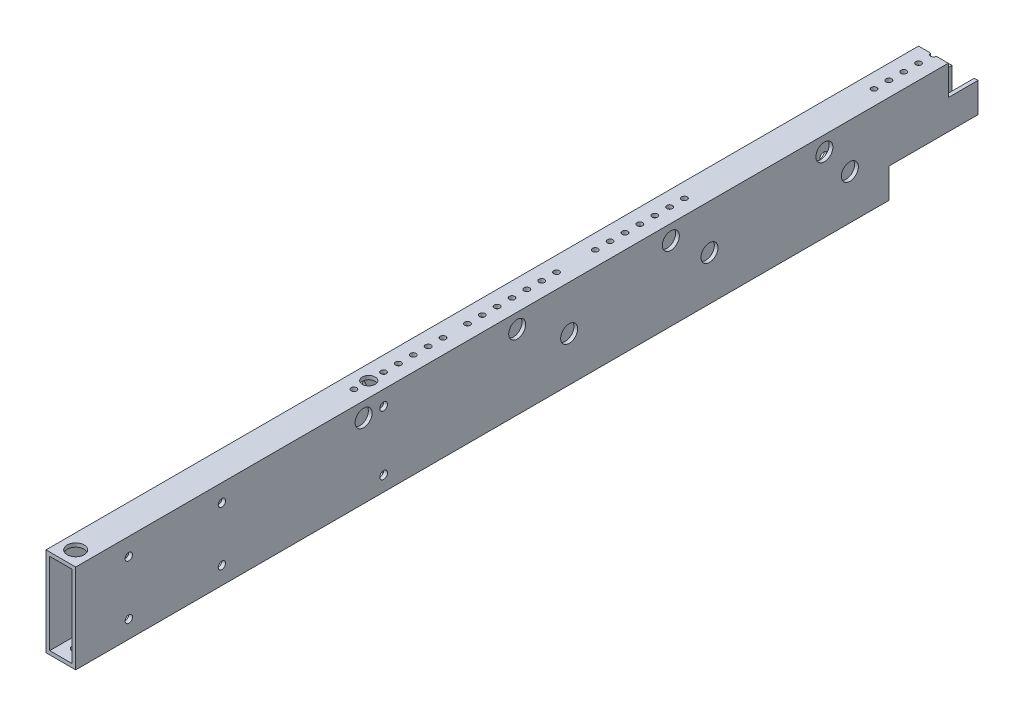
SolidWorks part; units mm, degrees
ref_plane "Front Plane" through (0, 0, 0) normal (0, 0, 1) x (1, 0, 0)
ref_plane "Top Plane" through (0, 0, 0) normal (0, 1, 0) x (1, 0, 0)
ref_plane "Right Plane" through (0, 0, 0) normal (1, 0, 0) x (0, 0, -1)
sketch "Sketch1" plane through (0, 0, 0) normal (0, 0, 1) x (1, 0, 0)
  line L1 (-12.7, -38.1) -> (12.7, -38.1)
  line L2 (-12.7, -38.1) -> (-12.7, 38.1)
  line L3 (-12.7, 38.1) -> (12.7, 38.1)
  line L4 (12.7, -38.1) -> (12.7, 38.1)
  line L5 (-12.7, -38.1) -> (12.7, 38.1) construction
  line L6 (-12.7, 38.1) -> (12.7, -38.1) construction
  point P0 (0, 0)
  dimension "D1" = 25.4
  dimension "D2" = 76.2
extrude "Boss-Extrude1" add sketch "Sketch1" along normal mid plane 771.398
shell "Shell1" thickness 3.175
sketch "Sketch2" plane through (12.7, 0, 0) normal (1, 0, 0) x (0, 0, -1)
  line L1 (385.699, -38.1) -> (309.499, -38.1)
  line L2 (385.699, -38.1) -> (385.699, -12.7)
  line L3 (385.699, -12.7) -> (309.499, -12.7)
  line L4 (309.499, -38.1) -> (309.499, -12.7)
  dimension "D1" = 25.4
  dimension "D2" = 76.2
extrude "Cut-Extrude1" cut sketch "Sketch2" against normal through all
sketch "Sketch3" plane through (12.7, 0, 0) normal (1, 0, 0) x (0, 0, -1)
  line L1 (385.699, 38.1) -> (360.299, 38.1)
  line L2 (385.699, 38.1) -> (385.699, 12.7)
  line L3 (385.699, 12.7) -> (360.299, 12.7)
  line L4 (360.299, 38.1) -> (360.299, 12.7)
  dimension "D1" = 25.4
extrude "Cut-Extrude2" cut sketch "Sketch3" against normal through all
sketch "Sketch4" plane through (0, 38.1, 0) normal (0, 1, 0) x (1, 0, 0)
  line L0 (-12.7, 360.299) -> (12.7, 360.299) construction
  circle A0 centre (0, 147.3945) radius 2.3812
  circle A1 centre (0, 134.6945) radius 2.3812
  circle A2 centre (0, 121.9945) radius 2.3812
  circle A3 centre (0, 109.2945) radius 2.3812
  circle A4 centre (0, 96.5945) radius 2.3812
  circle A5 centre (0, 83.8945) radius 2.3812
  circle A6 centre (0, 71.1945) radius 2.3812
  circle A7 centre (0, 38.0987) radius 2.3812
  circle A8 centre (0, 25.3987) radius 2.3813
  circle A9 centre (0, 12.6987) radius 2.3813
  circle A10 centre (0, -0.0013) radius 2.3813
  circle A11 centre (0, -12.7013) radius 2.3812
  circle A12 centre (0, -25.4013) radius 2.3812
  circle A13 centre (0, -38.1013) radius 2.3812
  circle A15 centre (0, -58.9932) radius 2.3812
  circle A16 centre (0, -71.6932) radius 2.3812
  circle A17 centre (0, -84.3932) radius 2.3812
  circle A18 centre (0, -97.0932) radius 2.3812
  circle A19 centre (0, -109.7932) radius 2.3812
  circle A20 centre (0, -122.4932) radius 2.3812
  circle A21 centre (0, -135.1932) radius 2.3813
  point P33 (0, 360.299)
  dimension "D1" = 4.7625
  dimension "D3" = 12.7
  dimension "D4" = 12.7
  dimension "D5" = 12.7
  dimension "D6" = 12.7
  dimension "D7" = 12.7
  dimension "D8" = 12.7
  dimension "D9" = 322.2003
  dimension "D10" = 12.7
  dimension "D11" = 12.7
  dimension "D12" = 12.7
  dimension "D13" = 12.7
  dimension "D14" = 12.7
  dimension "D15" = 12.7
  dimension "D16" = 12.7
  dimension "D17" = 419.2922
  dimension "D18" = 12.7
  dimension "D19" = 12.7
  dimension "D20" = 12.7
  dimension "D21" = 12.7
  dimension "D22" = 12.7
  dimension "D2" = 212.9045
extrude "Cut-Extrude3" cut sketch "Sketch4" against normal through all
sketch "Sketch5" plane through (0, 38.1, 0) normal (0, 1, 0) x (1, 0, 0)
  line L0 (-12.7, 360.299) -> (12.7, 360.299) construction
  circle A0 centre (0, 360.299) radius 2.3813
  circle A1 centre (0, 347.599) radius 2.3813
  circle A2 centre (0, 334.899) radius 2.3813
  circle A3 centre (0, 322.199) radius 2.3813
  circle A4 centre (0, 309.499) radius 2.3813
  dimension "D1" = 4.7625
  dimension "D3" = 12.7
  dimension "D4" = 12.7
  dimension "D5" = 12.7
  dimension "D8" = 0
  dimension "D2" = 12.7
extrude "Cut-Extrude4" cut sketch "Sketch5" against normal up to next
sketch "Sketch6" plane through (0, -38.1, 0) normal (0, -1, 0) x (1, 0, 0)
  line L0 (-12.7, -309.499) -> (12.7, -309.499) construction
  circle A0 centre (0, -309.499) radius 2.3813
  circle A1 centre (0, -296.799) radius 2.3813
  circle A2 centre (0, -284.099) radius 2.3813
  circle A3 centre (0, -258.699) radius 2.3813
  circle A6 centre (0, -271.399) radius 2.3813
  dimension "D1" = 4.7625
  dimension "D2" = 12.7
  dimension "D3" = 12.7
  dimension "D4" = 12.7
  dimension "D5" = 12.7
  dimension "D6" = 0
extrude "Cut-Extrude5" cut sketch "Sketch6" against normal up to next
sketch3d "3DSketch1" [suppressed]
  line L0 (0, 34.925, -109.2945) -> (0, 38.1, -109.2945) construction
  line L1 (0, 34.925, 97.0932) -> (0, 38.1, 97.0932) construction
  point P0 (0, 38.1, -109.2945)
  point P1 (0, 0, 0)
  point P4 (0, 38.1, 97.0932)
sketch "Sketch11" plane through (12.7, 0, 0) normal (1, 0, 0) x (0, 0, -1)
  point P0 (-340.3244, 23.1254)
  point P1 (-260.7244, 23.1254)
  point P3 (-260.7244, -23.1)
  point P5 (-340.3244, -23.1)
hole_wizard "CBORE for M6 Hex Head Bolt1" positions "Sketch19" profile "Sketch18" counterbore size "M6" standard "Lanco STD" end condition through all
sketch "Sketch19" plane through (-12.7, 0, 0) normal (-1, 0, 0) x (0, 0, 1)
  point P0 (260.7244, 23.1254)
  point P3 (260.7244, -23.1)
  point P6 (340.3244, 23.1254)
  point P9 (340.3244, -23.1)
sketch "Sketch18" plane through (-12.7, 23.1254, 260.7244) normal (0, 1, 0) x (0, 0, 1)
  line L0 (0, 0) -> (0, 25.4)
  line L1 (0, 25.4) -> (3.15, 25.4)
  line L3 (3.15, 25.4) -> (3.15, 4)
  line L4 (3.15, 4) -> (7.2735, 4)
  line L5 (7.2735, 4) -> (7.2735, 0)
  line L7 (7.2735, 0) -> (0, 0)
  line L11 (0, -6.35) -> (0, 107.95) construction
  dimension "Thru Hole Dia." = 6.3
  dimension "Thru Hole Depth" = 25.4
  dimension "C'Bore Dia." = 14.547
  dimension "C'Bore Depth" = 4
hole_wizard "CBORE for M6 Hex Head Cap Screw1" positions "Sketch21" profile "Sketch20" counterbore size "M6" standard "ANSI Metric" end condition through all
sketch "Sketch21" plane through (-12.7, 0, 0) normal (-1, 0, 0) x (0, 0, 1)
  line L0 (385.699, 38.1) -> (-360.299, 38.1) construction
  line L1 (385.699, 38.1) -> (385.699, -38.1) construction
  point P0 (122.4678, 25.4)
  point P2 (122.4678, -25.4)
  dimension "D1" = 12.7
  dimension "D2" = 63.5
  dimension "D3" = 263.2312
  dimension "D4" = 263.2312
sketch "Sketch20" plane through (-12.7, 25.4, 122.4678) normal (0, 1, 0) x (0, 0, 1)
  line L0 (0, 0) -> (0, 25.4)
  line L1 (0, 25.4) -> (3.3, 25.4)
  line L3 (3.3, 25.4) -> (3.3, 4.15)
  line L4 (3.3, 4.15) -> (7.275, 4.15)
  line L5 (7.275, 4.15) -> (7.275, 0)
  line L7 (7.275, 0) -> (0, 0)
  line L11 (0, -6.35) -> (0, 107.95) construction
  dimension "Thru Hole Dia." = 6.6
  dimension "Thru Hole Depth" = 25.4
  dimension "C'Bore Dia." = 14.55
  dimension "C'Bore Depth" = 4.15
hole_wizard "CBORE for M6 Hex Head Cap Screw2" positions "Sketch26" profile "Sketch25" counterbore size "M6" standard "ANSI Metric" end condition through all
sketch "Sketch26" plane through (0, 38.1, 0) normal (0, 1, 0) x (1, 0, 0)
  line L0 (12.7, -385.699) -> (-12.7, -385.699) construction
  point P0 (0, -372.999)
  dimension "D1" = 12.7
sketch "Sketch25" plane through (0, 38.1, 372.999) normal (1, 0, 0) x (0, 0, 1)
  line L0 (0, 0) -> (0, 76.2)
  line L1 (0, 76.2) -> (3.3, 76.2)
  line L3 (3.3, 76.2) -> (3.3, 4.15)
  line L4 (3.3, 4.15) -> (7.275, 4.15)
  line L5 (7.275, 4.15) -> (7.275, 0)
  line L7 (7.275, 0) -> (0, 0)
  line L11 (0, -6.35) -> (0, 107.95) construction
  dimension "Thru Hole Dia." = 6.6
  dimension "Thru Hole Depth" = 76.2
  dimension "C'Bore Dia." = 14.55
  dimension "C'Bore Depth" = 4.15
hole_wizard "CBORE for M6 Hex Head Cap Screw3" positions "Sketch28" profile "Sketch27" counterbore size "M6" standard "ANSI Metric" end condition through all
sketch "Sketch28" plane through (12.7, 0, 0) normal (1, 0, 0) x (0, 0, -1)
  point P9 (36.1449, 0)
  point P13 (156.1449, 0)
  point P15 (276.1449, 0)
sketch "Sketch27" plane through (12.7, 0, -36.1449) normal (0, 1, 0) x (0, 0, -1)
  line L0 (0, 0) -> (0, 25.4)
  line L1 (0, 25.4) -> (3.3, 25.4)
  line L3 (3.3, 25.4) -> (3.3, 4.15)
  line L4 (3.3, 4.15) -> (7.275, 4.15)
  line L5 (7.275, 4.15) -> (7.275, 0)
  line L7 (7.275, 0) -> (0, 0)
  line L11 (0, -6.35) -> (0, 107.95) construction
  dimension "Thru Hole Dia." = 6.6
  dimension "Thru Hole Depth" = 25.4
  dimension "C'Bore Dia." = 14.55
  dimension "C'Bore Depth" = 4.15
hole_wizard "CBORE for M6 Hex Head Bolt2" positions "Sketch32" profile "Sketch31" counterbore size "M6" standard "DIN" end condition through all
sketch "Sketch32" plane through (12.7, 0, 0) normal (1, 0, 0) x (0, 0, -1)
  line L0 (-385.699, 38.1) -> (360.299, 38.1) construction
  line L2 (385.699, -12.7) -> (385.699, 12.7) construction
  point P0 (254.381, 25.4)
  point P2 (123.063, 25.4)
  point P4 (-8.255, 25.4)
  point P6 (-139.573, 25.4)
  point P15 (385.699, 0)
  dimension "D1" = 12.7
  dimension "D2" = 131.318
  dimension "D3" = 131.318
  dimension "D4" = 131.318
  dimension "D5" = 131.318
sketch "Sketch31" plane through (12.7, 25.4, -254.381) normal (0, 1, 0) x (0, 0, -1)
  line L0 (0, 0) -> (0, 25.4)
  line L1 (0, 25.4) -> (3.15, 25.4)
  line L3 (3.15, 25.4) -> (3.15, 4)
  line L4 (3.15, 4) -> (7.2735, 4)
  line L5 (7.2735, 4) -> (7.2735, 0)
  line L7 (7.2735, 0) -> (0, 0)
  line L11 (0, -6.35) -> (0, 107.95) construction
  dimension "Thru Hole Dia." = 6.3
  dimension "Thru Hole Depth" = 25.4
  dimension "C'Bore Dia." = 14.547
  dimension "C'Bore Depth" = 4
hole_wizard "CBORE for M6 Hex Socket Head Cap Screw1" positions "Sketch34" profile "Sketch33" counterbore size "M6" standard "Lanco STD" end condition through all
sketch "Sketch34" plane through (0, 38.1, 0) normal (0, 1, 0) x (1, 0, 0)
  point P0 (0, -122.4932)
sketch "Sketch33" plane through (0, 38.1, 122.4932) normal (1, 0, 0) x (0, 0, 1)
  line L0 (0, 0) -> (0, 76.2)
  line L1 (0, 76.2) -> (3.2, 76.2)
  line L3 (3.2, 76.2) -> (3.2, 7)
  line L4 (3.2, 7) -> (5.5, 7)
  line L5 (5.5, 7) -> (5.5, 0)
  line L7 (5.5, 0) -> (0, 0)
  line L11 (0, -6.35) -> (0, 107.95) construction
  dimension "Thru Hole Dia." = 6.4
  dimension "Thru Hole Depth" = 76.2
  dimension "C'Bore Dia." = 11
  dimension "C'Bore Depth" = 7
equation "\"5.1`7\"=2.30417"
